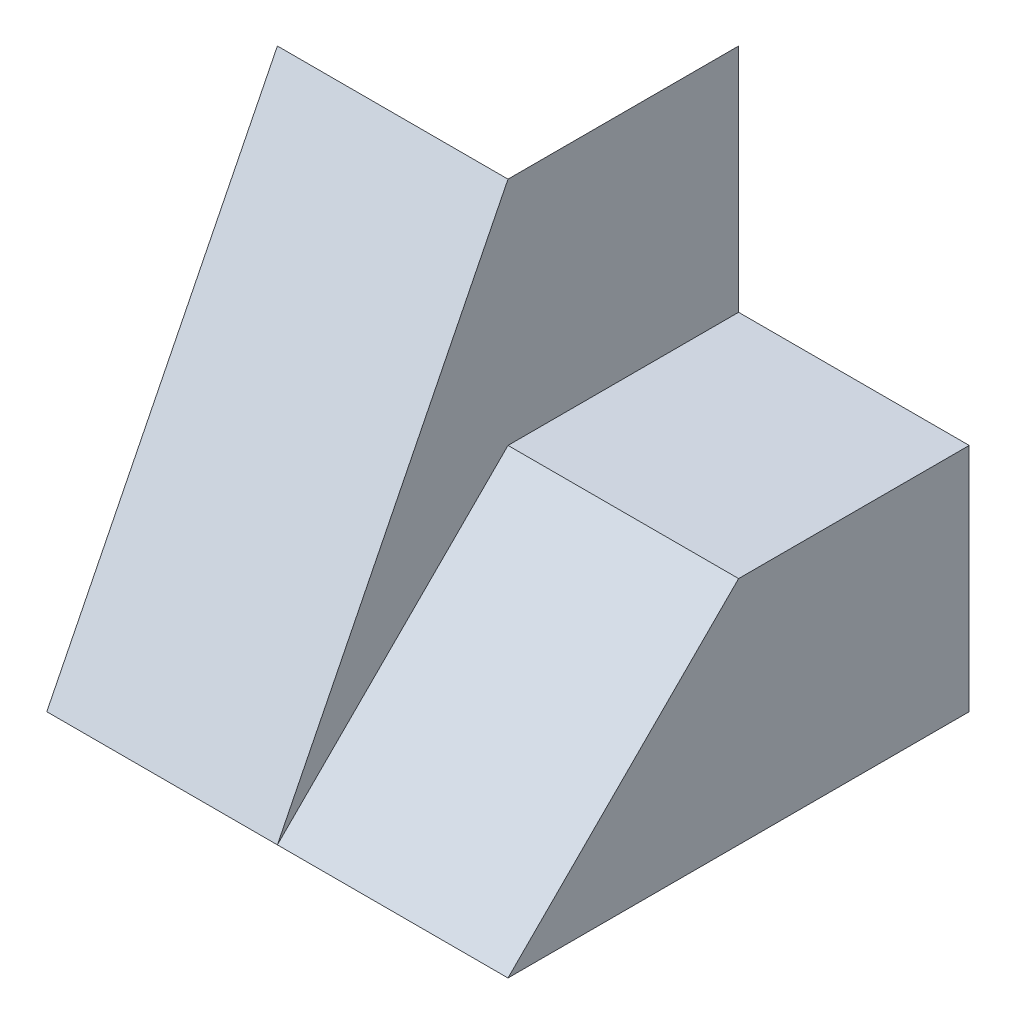
SolidWorks part; units mm, degrees
ref_plane "Front Plane" through (0, 0, 0) normal (0, 0, 1) x (1, 0, 0)
ref_plane "Top Plane" through (0, 0, 0) normal (0, 1, 0) x (1, 0, 0)
ref_plane "Right Plane" through (0, 0, 0) normal (1, 0, 0) x (0, 0, -1)
sketch "Sketch1" plane through (0, 0, 0) normal (0, 0, 1) x (1, 0, 0)
  line L1 (0, 0) -> (40, 0)
  line L2 (0, 0) -> (0, 40)
  line L3 (0, 40) -> (40, 40)
  line L4 (40, 0) -> (40, 40)
  dimension "D1" = 40
  dimension "D2" = 40
extrude "Boss-Extrude1" add sketch "Sketch1" along normal blind 40
sketch "Sketch2" plane through (0, 0, 40) normal (0, 0, 1) x (1, 0, 0)
  line L1 (40, 40) -> (20, 40)
  line L2 (40, 40) -> (40, 20)
  line L3 (40, 20) -> (20, 20)
  line L4 (20, 40) -> (20, 20)
  dimension "D1" = 20
  dimension "D2" = 20
extrude "Cut-Extrude1" cut sketch "Sketch2" against normal blind 40
sketch "Sketch3" plane through (40, 0, 0) normal (1, 0, 0) x (0, 0, -1)
  line L0 (-40, 0) -> (-20, 20)
  line L1 (0, 20) -> (-40, 20) construction
  line L2 (-20, 20) -> (-40, 20)
  line L3 (-40, 20) -> (-40, 0)
extrude "Cut-Extrude2" cut sketch "Sketch3" against normal blind 20
sketch "Sketch5" plane through (0, 0, 0) normal (0, 0, -1) x (-1, 0, 0)
  line L0 (-20, 40) -> (0, 20)
  line L1 (0, 40) -> (0, 0) construction
  line L2 (-20, 40) -> (0, 40)
  line L3 (0, 40) -> (0, 20)
extrude "Cut-Extrude4" cut sketch "Sketch5" against normal blind 20
sketch "Sketch6" plane through (0, 0, 0) normal (-1, 0, 0) x (0, 0, 1)
  line L0 (20, 40) -> (40, 0)
  line L1 (40, 0) -> (40, 40)
  line L2 (40, 40) -> (20, 40)
extrude "Cut-Extrude5" cut sketch "Sketch6" against normal blind 20
